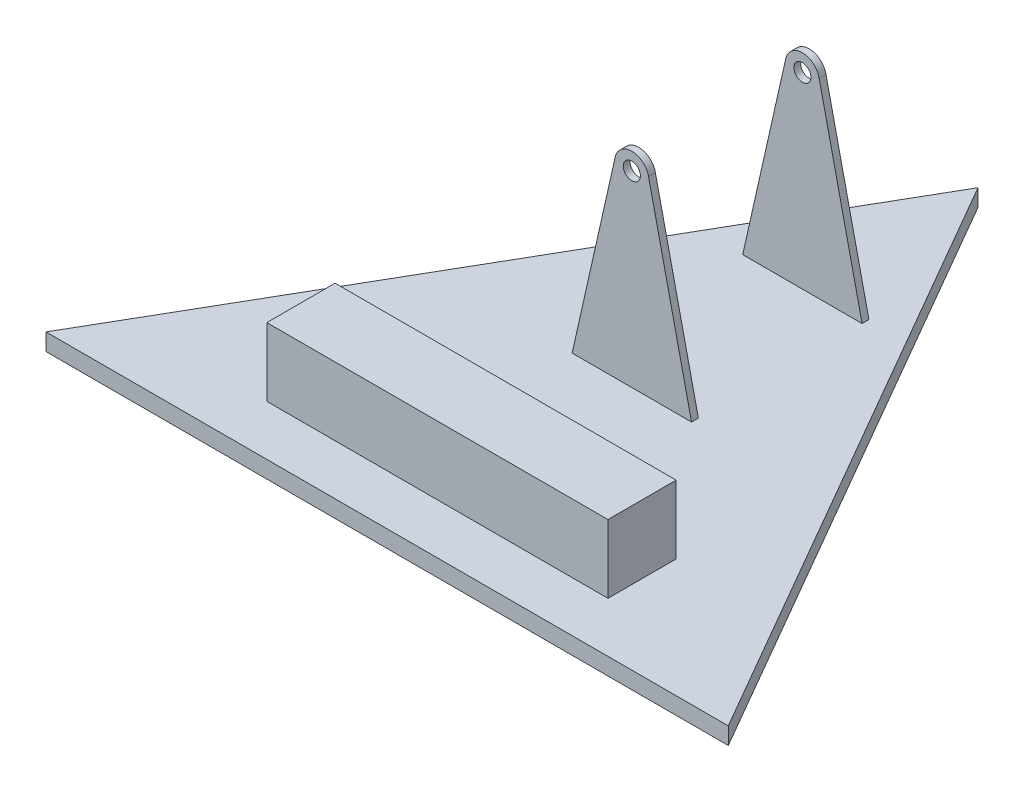
SolidWorks part; units mm, degrees
ref_plane "Front Plane" through (0, 0, 0) normal (0, 0, 1) x (1, 0, 0)
ref_plane "Top Plane" through (0, 0, 0) normal (0, 1, 0) x (1, 0, 0)
ref_plane "Right Plane" through (0, 0, 0) normal (1, 0, 0) x (0, 0, -1)
sketch "Sketch1" plane through (0, 0, 0) normal (0, 1, 0) x (1, 0, 0)
  line L1 (0, 115.4701) -> (-100, -57.735)
  line L2 (-100, -57.735) -> (100, -57.735)
  line L3 (100, -57.735) -> (0, 115.4701)
  circle A0 centre (0, 0) radius 57.735 construction
  point P1 (0, 0)
extrude "Boss-Extrude1" add sketch "Sketch1" along normal blind 5
sketch "Sketch2" plane through (0, 5, 0) normal (0, 1, 0) x (1, 0, 0)
  line L1 (-17.5, 64) -> (17.5, 64)
  line L2 (-17.5, 64) -> (-17.5, 66)
  line L3 (-17.5, 66) -> (17.5, 66)
  line L4 (17.5, 64) -> (17.5, 66)
  line L5 (-17.5, 64) -> (17.5, 66) construction
  line L6 (-17.5, 66) -> (17.5, 64) construction
  line L7 (-17.5, 14) -> (17.5, 14)
  line L8 (-17.5, 14) -> (-17.5, 16)
  line L9 (-17.5, 16) -> (17.5, 16)
  line L10 (17.5, 14) -> (17.5, 16)
  line L11 (-17.5, 14) -> (17.5, 16) construction
  line L12 (-17.5, 16) -> (17.5, 14) construction
  point P0 (0, 65)
  point P5 (0, 15)
extrude "Boss-Extrude2" add sketch "Sketch2" along normal blind 60
sketch "Sketch3" plane through (0, 0, -14) normal (0, 0, 1) x (1, 0, 0)
  line L0 (-17.5, 5) -> (-4.8556, 61.193)
  line L1 (17.5, 5) -> (4.8556, 61.193)
  line L2 (-17.5, 5) -> (-17.5, 65)
  line L3 (-17.5, 65) -> (17.5, 65)
  line L4 (-17.5, 65) -> (17.5, 65) construction
  line L5 (17.5, 65) -> (17.5, 5)
  line L6 (-17.5, 5) -> (-17.5, 65)
  line L7 (17.5, 65) -> (17.5, 5)
  line L8 (17.5, 5) -> (17.6459, 5.5416)
  circle A0 centre (0, 60) radius 5
  line M2 (17.5, 5) -> (17.5, 65)
  line M3 (17.5, 65) -> (-17.5, 65)
  line M4 (-17.5, 65) -> (-17.5, 5)
extrude "Cut-Extrude1" cut sketch "Sketch3" against normal blind 60 contours A0 L3 L0 M4 | A0 L1 M2 M3
sketch "Sketch4" plane through (0, 0, -14) normal (0, 0, 1) x (1, 0, 0)
  circle A0 centre (0, 60) radius 2.5
extrude "Cut-Extrude2" cut sketch "Sketch4" against normal blind 60
sketch "Sketch5" plane through (0, 5, 0) normal (0, 1, 0) x (1, 0, 0)
  line L1 (-50, -43) -> (50, -43)
  line L2 (-50, -43) -> (-50, -23)
  line L3 (-50, -23) -> (50, -23)
  line L4 (50, -43) -> (50, -23)
  line L5 (-50, -43) -> (50, -23) construction
  line L6 (-50, -23) -> (50, -43) construction
  point P0 (0, -33)
extrude "Boss-Extrude3" add sketch "Sketch5" along normal blind 20
